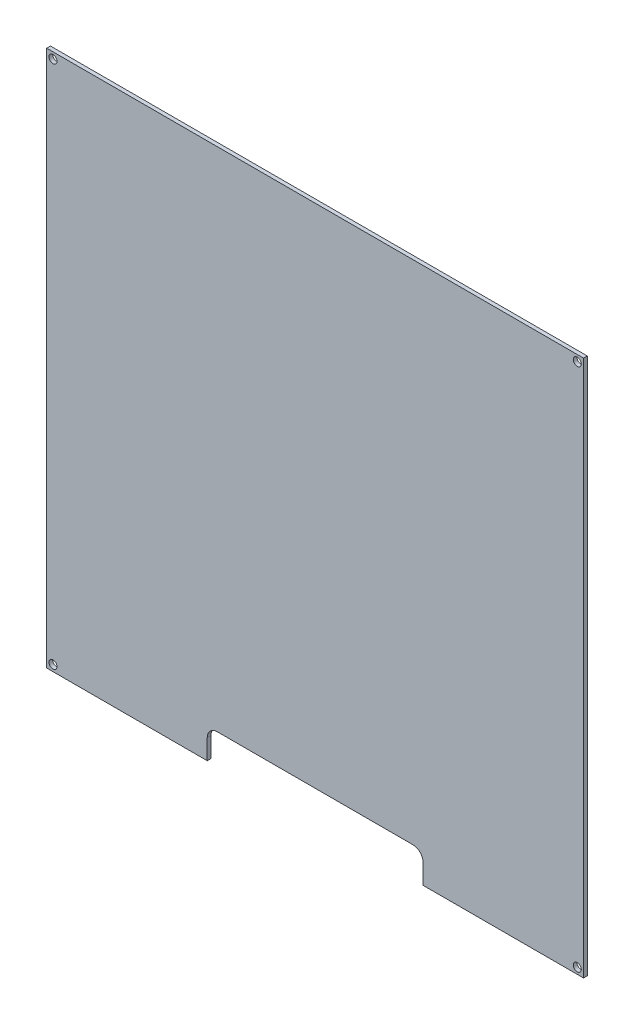
SolidWorks part; units mm, degrees
material "1060 Alloy"
ref_plane "Front Plane" through (0, 0, 0) normal (0, 0, 1) x (1, 0, 0)
ref_plane "Top Plane" through (0, 0, 0) normal (0, 1, 0) x (1, 0, 0)
ref_plane "Right Plane" through (0, 0, 0) normal (1, 0, 0) x (0, 0, -1)
sketch "Sketch1" plane through (0, 0, 0) normal (0, 0, 1) x (1, 0, 0)
  line L0 (-100, -100) -> (100, -100) construction
  line L1 (-100, -100) -> (-100, 100) construction
  line L2 (100, -100) -> (100, 100) construction
  line L3 (-100, 100) -> (100, 100) construction
  line L4 (-100, -100) -> (100, 100) construction
  line L5 (100, -100) -> (-100, 100) construction
  line L6 (-107, 0) -> (107, 0) construction
  line L7 (-107, -107) -> (107, -107)
  line L8 (-107, -107) -> (-107, 107)
  line L9 (-107, 107) -> (107, 107)
  line L10 (107, -107) -> (107, 107)
  line L11 (-107, -107) -> (107, 107) construction
  line L12 (-107, 107) -> (107, -107) construction
  circle A0 centre (-104.5, 104.5) radius 1.6
  circle A1 centre (104.5, 104.5) radius 1.6
  circle A2 centre (0, -104.5) radius 1.6
  circle A3 centre (104.5, -104.5) radius 1.6
  circle A4 centre (-104.5, -104.5) radius 1.6
  point P0 (0, 0)
  point P1 (0, 0)
  dimension "D4" = 3.2
  dimension "D1" = 209
  dimension "D2" = 200
  dimension "D3" = 214
  dimension "D5" = 209
extrude "Boss-Extrude1" add sketch "Sketch1" along normal blind 1.5
sketch "Sketch2" plane through (0, 0, 1.5) normal (0, 0, 1) x (1, 0, 0)
  line L0 (-107, -107) -> (107, -107) construction
  line L1 (-43, -107) -> (43, -107)
  line L2 (-43, -107) -> (-43, -95)
  line L3 (-43, -95) -> (43, -95)
  line L4 (43, -107) -> (43, -95)
  dimension "D1" = 12
  dimension "D2" = 43
  dimension "D3" = 86
extrude "Cut-Extrude1" cut sketch "Sketch2" against normal through all
fillet "Fillet1" radius 4 2 edges at (43, -95, 0.75) (-43, -95, 0.75)
